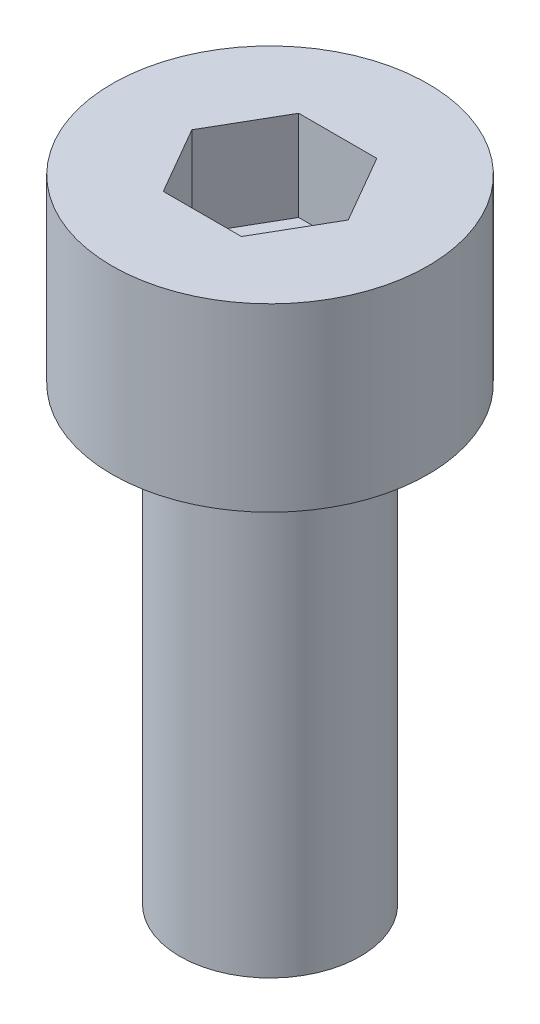
SolidWorks part; units mm, degrees
material "AISI 304"
ref_plane "前视基准面" through (0, 0, 0) normal (0, 0, 1) x (1, 0, 0)
ref_plane "上视基准面" through (0, 0, 0) normal (0, 1, 0) x (1, 0, 0)
ref_plane "右视基准面" through (0, 0, 0) normal (1, 0, 0) x (0, 0, -1)
sketch "草图1" plane through (0, 0, 0) normal (0, 1, 0) x (1, 0, 0)
  circle A0 centre (0, 0) radius 3.5
  dimension "D1" = 7
extrude "杯头" add sketch "草图1" along normal blind 4
sketch "草图2" plane through (0, 4, 0) normal (0, 1, 0) x (1, 0, 0)
  line L1 (1.7321, 0) -> (0.866, 1.5)
  line L2 (0.866, 1.5) -> (-0.866, 1.5)
  line L3 (-0.866, 1.5) -> (-1.7321, 0)
  line L4 (-1.7321, 0) -> (-0.866, -1.5)
  line L5 (-0.866, -1.5) -> (0.866, -1.5)
  line L6 (0.866, -1.5) -> (1.7321, 0)
  circle A0 centre (0, 0) radius 1.5 construction
  dimension "D1" = 3
extrude "内六角口" cut sketch "草图2" against normal blind 2
sketch "草图3" plane through (0, 0, 0) normal (0, -1, 0) x (1, 0, 0)
  circle A0 centre (0, 0) radius 2
  dimension "D1" = 4
extrude "螺纹长度" add sketch "草图3" along normal blind 10
